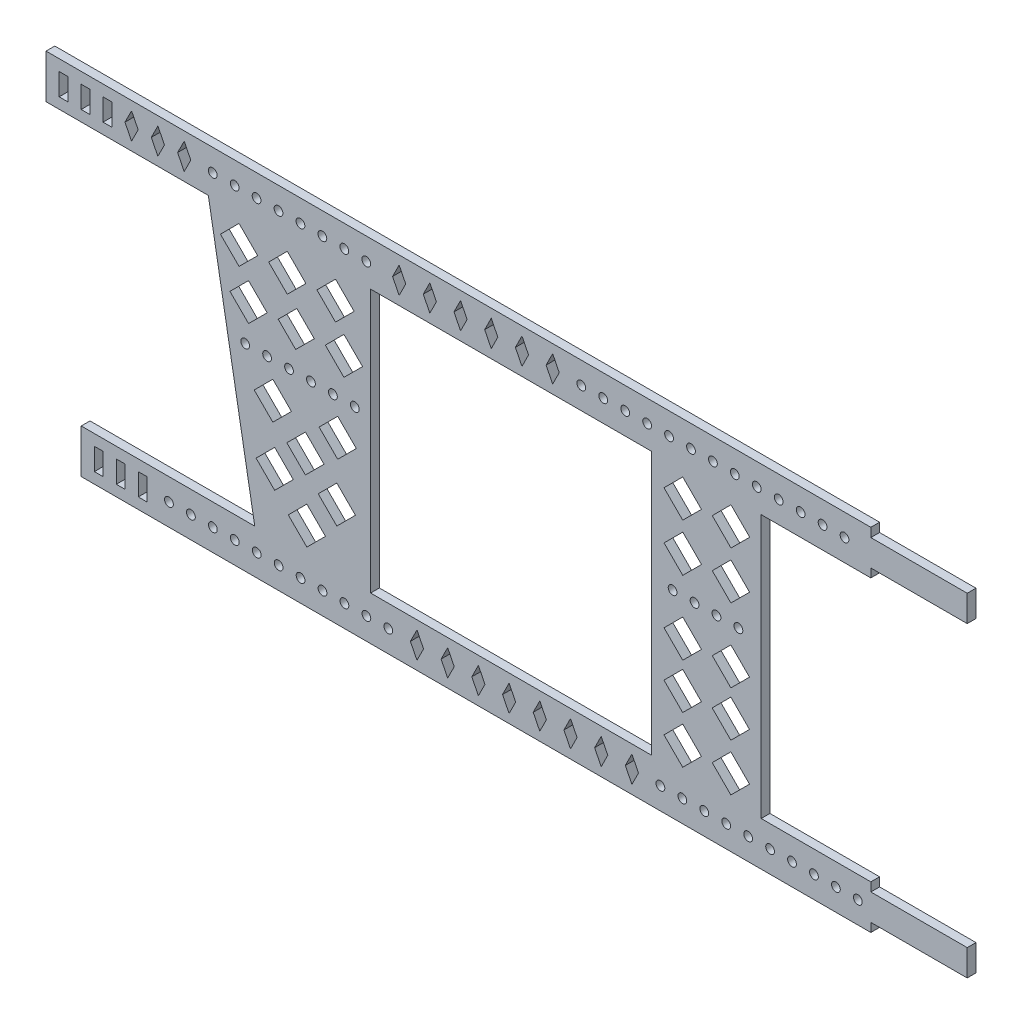
SolidWorks part; units mm, degrees
ref_plane "前视基准面" through (0, 0, 0) normal (0, 0, 1) x (1, 0, 0)
ref_plane "上视基准面" through (0, 0, 0) normal (0, 1, 0) x (1, 0, 0)
ref_plane "右视基准面" through (0, 0, 0) normal (1, 0, 0) x (0, 0, -1)
other "Configuration Table"
sketch "草图1" plane through (0, 0, 0) normal (0, 0, 1) x (1, 0, 0)
  line L4 (-82, 0.0001) -> (-80.5, 3.0002)
  line L11 (0, 0) -> (121.948, 0) construction
  line L17 (-82, 0.0001) -> (-80.4999, -3.0001)
  line L18 (-80.5, 3.0002) -> (-78.9999, 0)
  line L44 (-80.4999, -3.0001) -> (-78.9999, 0)
  line L49 (-76, 0.0001) -> (-74.5, 3.0002)
  line L50 (-92, 2.5) -> (-92, -2.5)
  line L51 (-99.9999, 5.0353) -> (88.0306, 5.0353)
  line L52 (-99.9999, 5.0353) -> (-99.9999, -4.9647)
  line L53 (-99.9999, -4.9647) -> (88.0306, -4.9647)
  line L54 (110.0001, 3) -> (110.0001, -3)
  line L55 (-97, 2.5) -> (-95, 2.5)
  line L56 (-97, 2.5) -> (-97, -2.5)
  line L57 (-97, -2.5) -> (-95, -2.5)
  line L58 (-95, 2.5) -> (-95, -2.5)
  line L59 (-97, 2.5) -> (-95, -2.5) construction
  line L60 (-97, -2.5) -> (-95, 2.5) construction
  line L61 (-92, 2.5) -> (-90, 2.5)
  line L62 (-90, 2.5) -> (-90, -2.5)
  line L63 (-92, -2.5) -> (-90, -2.5)
  line L64 (-87, 2.5) -> (-87, -2.5)
  line L65 (-87, 2.5) -> (-85, 2.5)
  line L66 (-85, 2.5) -> (-85, -2.5)
  line L67 (-87, -2.5) -> (-85, -2.5)
  line L72 (-76, 0.0001) -> (-74.4999, -3.0001)
  line L73 (-62.9999, -4.9647) -> (-52.4203, -64.9647)
  line L74 (-52.4203, -64.9647) -> (-25.9999, -64.9647)
  line L75 (-25.9999, -4.9647) -> (-25.9999, -64.9647)
  line L77 (-74.4999, -3.0001) -> (-72.9999, 0)
  line L78 (-74.5, 3.0002) -> (-72.9999, 0)
  line L79 (-70, 0.0001) -> (-68.5, 3.0002)
  line L80 (-70, 0.0001) -> (-68.4999, -3.0001)
  line L81 (-68.4999, -3.0001) -> (-66.9999, 0)
  line L82 (-68.5, 3.0002) -> (-66.9999, 0)
  line L83 (-61.9999, 0) -> (-56.9999, 0) construction
  line L84 (-62.9999, 0) -> (-62.9999, -4.9647) construction
  line L85 (-25.9999, 0) -> (-25.9999, -8.8507) construction
  line L86 (-21, 0.04) -> (-19.5, 3.04)
  line L87 (-21, 0.04) -> (-19.5, -2.96)
  line L88 (-19.5, -2.96) -> (-18, 0.04)
  line L89 (-19.5, 3.04) -> (-18, 0.04)
  line L90 (-14, 0.04) -> (-12.5, 3.04)
  line L91 (-12.5, 3.04) -> (-11, 0.04)
  line L92 (-12.5, -2.96) -> (-11, 0.04)
  line L93 (-14, 0.04) -> (-12.5, -2.96)
  line L94 (-7, 0.04) -> (-5.5, 3.04)
  line L95 (-5.5, 3.04) -> (-4, 0.04)
  line L96 (-5.5, -2.96) -> (-4, 0.04)
  line L97 (-7, 0.04) -> (-5.5, -2.96)
  line L98 (0, 0.04) -> (1.5, 3.04)
  line L99 (1.5, 3.04) -> (3, 0.04)
  line L100 (1.5, -2.96) -> (3, 0.04)
  line L101 (0, 0.04) -> (1.5, -2.96)
  line L102 (7, 0.04) -> (8.5, 3.04)
  line L103 (8.5, 3.04) -> (10, 0.04)
  line L104 (8.5, -2.96) -> (10, 0.04)
  line L105 (7, 0.04) -> (8.5, -2.96)
  line L106 (14, 0.04) -> (15.5, 3.04)
  line L107 (15.5, 3.04) -> (17, 0.04)
  line L108 (15.5, -2.96) -> (17, 0.04)
  line L109 (14, 0.04) -> (15.5, -2.96)
  line L110 (-21, 0.04) -> (-14, 0.04) construction
  line L111 (22.0306, 0.0331) -> (27.0306, 0.0331) construction
  line L112 (88.0306, 6.2733) -> (88.0306, -6.7746) construction
  line L113 (88.0306, 3) -> (110.0001, 3)
  line L114 (88.0306, -3) -> (110.0001, -3)
  line L115 (88.0306, 5.0353) -> (88.0306, 3)
  line L116 (88.0306, -3) -> (88.0306, -4.9647)
  line L117 (38.0306, 0.0331) -> (38.0306, -8.8507) construction
  line L118 (63.0306, 0.0331) -> (63.0306, -8.8507) construction
  line L138 (-55.9986, -6.9922) -> (-60.2412, -11.2349)
  line L143 (-44.9986, -6.9922) -> (-49.2412, -11.2349)
  line L144 (-44.9986, -6.9922) -> (-40.7559, -11.2349)
  line L145 (-55.9986, -6.9922) -> (-51.7559, -11.2349)
  line L146 (-60.2412, -11.2349) -> (-55.9986, -15.4775)
  line L147 (-51.7559, -11.2349) -> (-55.9986, -15.4775)
  line L148 (-40.7559, -11.2349) -> (-44.9986, -15.4775)
  line L149 (-49.2412, -11.2349) -> (-44.9986, -15.4775)
  line L150 (-33.9986, -6.9922) -> (-38.2412, -11.2349)
  line L151 (-33.9986, -6.9922) -> (-29.7559, -11.2349)
  line L152 (-29.7559, -11.2349) -> (-33.9986, -15.4775)
  line L153 (-38.2412, -11.2349) -> (-33.9986, -15.4775)
  line L154 (-55.9986, -6.9922) -> (-44.9986, -6.9922) construction
  line L167 (-53.8279, -17.1935) -> (-58.0705, -21.4361)
  line L168 (-42.8279, -17.1935) -> (-47.0705, -21.4361)
  line L169 (-42.8279, -17.1935) -> (-38.8399, -21.1815)
  line L170 (-53.8279, -17.1935) -> (-49.5852, -21.4361)
  line L171 (-58.0705, -21.4361) -> (-53.8279, -25.6788)
  line L172 (-49.5852, -21.4361) -> (-53.8279, -25.6788)
  line L173 (-38.8399, -21.1815) -> (-43.0826, -25.4241)
  line L174 (-47.0705, -21.4361) -> (-43.0826, -25.4241)
  line L175 (-32.0826, -16.9388) -> (-36.3252, -21.1815)
  line L176 (-32.0826, -16.9388) -> (-27.8399, -21.1815)
  line L177 (-27.8399, -21.1815) -> (-32.0826, -25.4241)
  line L178 (-36.3252, -21.1815) -> (-32.0826, -25.4241)
  line L179 (-53.8279, -17.1935) -> (-42.8279, -17.1935) construction
  line L180 (63.0306, -29.9647) -> (-66.6645, -29.9647) construction
  line L181 (-54.5983, -30) -> (-49.5983, -30) construction
  line L186 (-48.294, -33.8993) -> (-52.5367, -38.1419)
  line L187 (-52.5367, -38.1419) -> (-48.294, -42.3846)
  line L188 (-44.0514, -38.1419) -> (-48.294, -42.3846)
  line L189 (-48.294, -33.8993) -> (-44.0514, -38.1419)
  line L190 (-33.5054, -33.8232) -> (-37.7481, -38.0658)
  line L191 (-37.7481, -38.0658) -> (-33.5054, -42.3084)
  line L192 (-29.2628, -38.0658) -> (-33.5054, -42.3084)
  line L193 (-33.5054, -33.8232) -> (-29.2628, -38.0658)
  line L195 (-47.8719, -47.1411) -> (-52.1146, -51.3837)
  line L196 (-52.1146, -51.3837) -> (-47.8719, -55.6263)
  line L197 (-43.6293, -51.3837) -> (-47.8719, -55.6263)
  line L198 (-47.8719, -47.1411) -> (-43.6293, -51.3837)
  line L199 (-40.8637, -40.6049) -> (-45.1063, -44.8475)
  line L200 (-45.1063, -44.8475) -> (-40.8637, -49.0901)
  line L201 (-36.6211, -44.8475) -> (-40.8637, -49.0901)
  line L202 (-40.8637, -40.6049) -> (-36.6211, -44.8475)
  line L203 (-40.5381, -54.6754) -> (-44.7807, -58.9181)
  line L204 (-44.7807, -58.9181) -> (-40.5381, -63.1607)
  line L205 (-36.2954, -58.9181) -> (-40.5381, -63.1607)
  line L206 (-40.5381, -54.6754) -> (-36.2954, -58.9181)
  line L207 (-33.7086, -47.1027) -> (-37.9513, -51.3454)
  line L208 (-37.9513, -51.3454) -> (-33.7086, -55.588)
  line L209 (-29.466, -51.3454) -> (-33.7086, -55.588)
  line L210 (-33.7086, -47.1027) -> (-29.466, -51.3454)
  line L215 (-52.4203, -64.9647) -> (-91.9694, -64.9647)
  line L216 (-25.9999, -64.9647) -> (63.0306, -64.9647)
  line L217 (38.0306, -4.9647) -> (38.0306, -64.9647)
  line L218 (63.0306, 0) -> (63.0306, -64.9647)
  line L219 (42.8446, -29.9642) -> (47.8446, -29.9642) construction
  line L220 (45.1493, -6.4688) -> (40.8811, -10.737)
  line L221 (40.8811, -10.737) -> (45.1493, -15.0051)
  line L222 (49.4174, -10.737) -> (45.1493, -15.0051)
  line L223 (45.1493, -6.4688) -> (49.4174, -10.737)
  line L224 (56.1493, -6.4688) -> (51.8811, -10.737)
  line L225 (51.8811, -10.737) -> (56.1493, -15.0051)
  line L226 (60.4174, -10.737) -> (56.1493, -15.0051)
  line L227 (56.1493, -6.4688) -> (60.4174, -10.737)
  line L228 (45.1493, -6.4688) -> (56.1493, -6.4688) construction
  line L229 (45.1571, -17.3518) -> (40.889, -21.62)
  line L230 (40.889, -21.62) -> (45.1571, -25.8881)
  line L231 (49.4253, -21.62) -> (45.1571, -25.8881)
  line L232 (45.1571, -17.3518) -> (49.4253, -21.62)
  line L233 (56.1316, -17.3518) -> (51.8762, -21.6072)
  line L234 (51.8762, -21.6072) -> (56.1316, -25.8626)
  line L235 (60.387, -21.6072) -> (56.1316, -25.8626)
  line L236 (56.1316, -17.3518) -> (60.387, -21.6072)
  line L237 (45.1571, -17.3518) -> (56.1316, -17.3518) construction
  line L238 (45.1553, -34.115) -> (40.8872, -38.3832)
  line L239 (40.8872, -38.3832) -> (45.1553, -42.6513)
  line L240 (49.4235, -38.3832) -> (45.1553, -42.6513)
  line L241 (45.1553, -34.115) -> (49.4235, -38.3832)
  line L242 (56.1298, -34.1405) -> (51.8872, -38.3832)
  line L243 (51.8872, -38.3832) -> (56.1298, -42.6258)
  line L244 (60.3725, -38.3832) -> (56.1298, -42.6258)
  line L245 (56.1298, -34.1405) -> (60.3725, -38.3832)
  line L246 (45.1553, -34.115) -> (56.1298, -34.1405) construction
  line L247 (45.142, -44.4521) -> (40.8738, -48.7203)
  line L248 (40.8738, -48.7203) -> (45.142, -52.9884)
  line L249 (49.4101, -48.7203) -> (45.142, -52.9884)
  line L250 (45.142, -44.4521) -> (49.4101, -48.7203)
  line L251 (56.1165, -44.4521) -> (51.8611, -48.7075)
  line L252 (51.8611, -48.7075) -> (56.1165, -52.9629)
  line L253 (60.3719, -48.7075) -> (56.1165, -52.9629)
  line L254 (56.1165, -44.4521) -> (60.3719, -48.7075)
  line L255 (45.142, -44.4521) -> (56.1165, -44.4521) construction
  line L256 (45.146, -55.2548) -> (40.8778, -59.523)
  line L257 (40.8778, -59.523) -> (45.146, -63.7911)
  line L258 (49.4141, -59.523) -> (45.146, -63.7911)
  line L259 (45.146, -55.2548) -> (49.4141, -59.523)
  line L260 (56.1205, -55.2548) -> (51.8651, -59.5102)
  line L261 (51.8651, -59.5102) -> (56.1205, -63.7656)
  line L262 (60.3759, -59.5102) -> (56.1205, -63.7656)
  line L263 (56.1205, -55.2548) -> (60.3759, -59.5102)
  line L264 (45.146, -55.2548) -> (56.1205, -55.2548) construction
  line L265 (45.1493, -6.4943) -> (45.1493, -76.2288) construction
  line L266 (0, 0.04) -> (0, -21.1815) construction
  line L267 (-91.9694, -64.9647) -> (-91.9694, -74.9647)
  line L268 (-91.9694, -74.9647) -> (88.0306, -74.9647)
  line L269 (63.0306, -64.9647) -> (88.0306, -64.9647)
  line L270 (88.0306, -64.9647) -> (88.0306, -66.9647)
  line L271 (88.0306, -66.9647) -> (110.0001, -66.9647)
  line L272 (110.0001, -66.9647) -> (110.0001, -72.9647)
  line L273 (110.0001, -72.9647) -> (88.0306, -72.9647)
  line L274 (88.0306, -72.9647) -> (88.0306, -74.9647)
  line L275 (-83.9694, -67.4775) -> (-81.9694, -67.4775)
  line L276 (47.8446, -29.9642) -> (52.8446, -29.9642) construction
  line L277 (52.8446, -29.9642) -> (50.3446, -29.9642) construction
  line L278 (50.3446, -29.9642) -> (50.3446, -32.9055) construction
  line L279 (40.0646, -69.9647) -> (45.0646, -69.9647) construction
  line L283 (-88.9694, -67.4775) -> (-86.9694, -67.4775)
  line L284 (-88.9694, -67.4775) -> (-88.9694, -72.4775)
  line L285 (-88.9694, -72.4775) -> (-86.9694, -72.4775)
  line L286 (-86.9694, -67.4775) -> (-86.9694, -72.4775)
  line L287 (-88.9694, -67.4775) -> (-86.9694, -72.4775) construction
  line L288 (-88.9694, -72.4775) -> (-86.9694, -67.4775) construction
  line L304 (-81.9694, -67.4775) -> (-81.9694, -72.4775)
  line L305 (-83.9694, -72.4775) -> (-81.9694, -72.4775)
  line L306 (-83.9694, -67.4775) -> (-83.9694, -72.4775)
  line L307 (-78.9694, -67.4775) -> (-76.9694, -67.4775)
  line L308 (-76.9694, -67.4775) -> (-76.9694, -72.4775)
  line L309 (-78.9694, -72.4775) -> (-76.9694, -72.4775)
  line L310 (-78.9694, -67.4775) -> (-78.9694, -72.4775)
  line L311 (-88.9694, -67.4775) -> (-83.9694, -67.4775) construction
  line L312 (-90.9389, -69.9647) -> (-66.4869, -69.9647) construction
  line L313 (-71.9694, -69.9647) -> (-66.9694, -69.9647) construction
  line L314 (-16.9354, -69.9662) -> (-15.4354, -66.9662)
  line L315 (-15.4354, -66.9662) -> (-13.9354, -69.9662)
  line L316 (-15.4354, -72.9662) -> (-13.9354, -69.9662)
  line L317 (-16.9354, -69.9662) -> (-15.4354, -72.9662)
  line L318 (-9.9354, -69.9662) -> (-8.4354, -66.9662)
  line L319 (-8.4354, -66.9662) -> (-6.9354, -69.9662)
  line L320 (-8.4354, -72.9662) -> (-6.9354, -69.9662)
  line L321 (-9.9354, -69.9662) -> (-8.4354, -72.9662)
  line L322 (-2.9354, -69.9662) -> (-1.4354, -66.9662)
  line L323 (-1.4354, -66.9662) -> (0.0646, -69.9662)
  line L324 (-1.4354, -72.9662) -> (0.0646, -69.9662)
  line L325 (-2.9354, -69.9662) -> (-1.4354, -72.9662)
  line L326 (4.0646, -69.9662) -> (5.5646, -66.9662)
  line L327 (5.5646, -66.9662) -> (7.0646, -69.9662)
  line L328 (5.5646, -72.9662) -> (7.0646, -69.9662)
  line L329 (4.0646, -69.9662) -> (5.5646, -72.9662)
  line L330 (11.0646, -69.9662) -> (12.5646, -66.9662)
  line L331 (12.5646, -66.9662) -> (14.0646, -69.9662)
  line L332 (12.5646, -72.9662) -> (14.0646, -69.9662)
  line L333 (11.0646, -69.9662) -> (12.5646, -72.9662)
  line L334 (18.0646, -69.9662) -> (19.5646, -66.9662)
  line L335 (19.5646, -66.9662) -> (21.0646, -69.9662)
  line L336 (19.5646, -72.9662) -> (21.0646, -69.9662)
  line L337 (18.0646, -69.9662) -> (19.5646, -72.9662)
  line L338 (25.0646, -69.9662) -> (26.5646, -66.9662)
  line L339 (26.5646, -66.9662) -> (28.0646, -69.9662)
  line L340 (26.5646, -72.9662) -> (28.0646, -69.9662)
  line L341 (25.0646, -69.9662) -> (26.5646, -72.9662)
  line L342 (32.0646, -69.9662) -> (33.5646, -66.9662)
  line L343 (33.5646, -66.9662) -> (35.0646, -69.9662)
  line L344 (33.5646, -72.9662) -> (35.0646, -69.9662)
  line L345 (32.0646, -69.9662) -> (33.5646, -72.9662)
  line L346 (-16.9354, -69.9662) -> (-9.9354, -69.9662) construction
  circle A0 centre (-61.9999, 0) radius 1
  circle A1 centre (-56.9999, 0) radius 1
  circle A2 centre (-51.9999, 0) radius 1
  circle A3 centre (-46.9999, 0) radius 1
  circle A4 centre (-41.9999, 0) radius 1
  circle A5 centre (-36.9999, 0) radius 1
  circle A6 centre (-31.9999, 0) radius 1
  circle A7 centre (-26.9999, 0) radius 1
  circle A8 centre (22.0306, 0.0331) radius 1
  circle A9 centre (27.0306, 0.0331) radius 1
  circle A10 centre (32.0306, 0.0331) radius 1
  circle A11 centre (37.0306, 0.0331) radius 1
  circle A12 centre (42.0306, 0.0331) radius 1
  circle A13 centre (47.0306, 0.0331) radius 1
  circle A14 centre (52.0306, 0.0331) radius 1
  circle A15 centre (57.0306, 0.0331) radius 1
  circle A16 centre (62.0306, 0.0331) radius 1
  circle A17 centre (67.0306, 0.0331) radius 1
  circle A18 centre (72.0306, 0.0331) radius 1
  circle A19 centre (77.0306, 0.0331) radius 1
  circle A20 centre (82.0306, 0.0331) radius 1
  circle A21 centre (-55.9986, -11.2349) radius 4.2426 construction
  circle A23 centre (-53.8279, -21.4361) radius 4.2426 construction
  circle A24 centre (-54.5983, -30) radius 1
  circle A25 centre (-49.5983, -30) radius 1
  circle A26 centre (-44.5983, -30) radius 1
  circle A27 centre (-39.5983, -30) radius 1
  circle A28 centre (-34.5983, -30) radius 1
  circle A29 centre (-29.5983, -30) radius 1
  circle A30 centre (42.8446, -29.9642) radius 1
  circle A31 centre (47.8446, -29.9642) radius 1
  circle A32 centre (52.8446, -29.9642) radius 1
  circle A33 centre (57.8446, -29.9642) radius 1
  circle A38 centre (-71.9694, -69.9647) radius 1
  circle A39 centre (-66.9694, -69.9647) radius 1
  circle A40 centre (-61.9694, -69.9647) radius 1
  circle A41 centre (-56.9694, -69.9647) radius 1
  circle A42 centre (-51.9694, -69.9647) radius 1
  circle A43 centre (-46.9694, -69.9647) radius 1
  circle A44 centre (-41.9694, -69.9647) radius 1
  circle A45 centre (-36.9694, -69.9647) radius 1
  circle A46 centre (-31.9694, -69.9647) radius 1
  circle A47 centre (-26.9694, -69.9647) radius 1
  circle A48 centre (-21.9694, -69.9647) radius 1
  circle A50 centre (-16.9694, -69.9647) radius 1 [skipped]
  circle A51 centre (40.0646, -69.9647) radius 1
  circle A52 centre (45.0646, -69.9647) radius 1
  circle A53 centre (50.0646, -69.9647) radius 1
  circle A54 centre (55.0646, -69.9647) radius 1
  circle A55 centre (60.0646, -69.9647) radius 1
  circle A56 centre (65.0646, -69.9647) radius 1
  circle A57 centre (70.0646, -69.9647) radius 1
  circle A58 centre (75.0646, -69.9647) radius 1
  circle A59 centre (80.0646, -69.9647) radius 1
  circle A60 centre (85.0646, -69.9647) radius 1
  point P0 (0, 0)
  point P11 (-61.9999, 0)
  point P32 (0, 0)
  point P33 (-96, 0)
  point P35 (0, 0)
  point P40 (-99.9999, 0.0353)
  point P41 (-96, 0)
  point P46 (-82, 0.0001)
  point P60 (-20.9999, 0)
  point P74 (22, 0)
  point P100 (88.0306, 0)
  point P128 (88.0306, -3)
  point P129 (88.0306, 3)
  point P130 (88.0306, 0)
  point P133 (88.0306, 5.0353)
  point P136 (88.0306, -4.9647)
  point P169 (-25.9999, -29.9647)
  point P172 (-54.5983, -29.9647)
  point P225 (42.8454, -29.9647)
  point P291 (88.0306, -64.9647)
  point P307 (40.0646, -69.9647)
  point P319 (-87.9694, -69.9775)
  point P320 (-87.9694, -69.9775)
  point P332 (-71.9694, -69.9647)
  point P333 (-91.9694, -69.9647)
  dimension "D7" = 2
  dimension "D32" = 8.4853
  dimension "D34" = 8.4853
  dimension "D43" = 11
  dimension "D58" = 2
  dimension "D64" = 2
  dimension "D2" = 3
  dimension "D3" = 3
  dimension "D4" = 3
  dimension "D5" = 33
  dimension "D8" = 5
  dimension "D9" = 210
  dimension "D10" = 10
  dimension "D11" = 4
  dimension "D12" = 2
  dimension "D13" = 5
  dimension "D15" = 8
  dimension "D6" = 5
  dimension "D16" = 5
  dimension "D18" = 7
  dimension "D19" = 5
  dimension "D20" = 5
  dimension "D21" = 182.0305
  dimension "D22" = 6
  dimension "D23" = 3
  dimension "D24" = 3
  dimension "D25" = 21.9695
  dimension "D26" = 137.0305
  dimension "D28" = 100
  dimension "D29" = 60
  dimension "D30" = 11
  dimension "D31" = 3
  dimension "D33" = 6
  dimension "D35" = 6
  dimension "D36" = 5
  dimension "D37" = 25
  dimension "D38" = 6
  dimension "D39" = 6
  dimension "D41" = 5
  dimension "D44" = 2
  dimension "D42" = 60
  dimension "D45" = 10
  dimension "D46" = 2
  dimension "D47" = 180
  dimension "D48" = 2
  dimension "D49" = 21.9695
  dimension "D50" = 6
  dimension "D52" = 5
  dimension "D53" = 4
  dimension "D54" = 5
  dimension "D55" = 5
  dimension "D57" = 5
  dimension "D59" = 5
  dimension "D61" = 12
  dimension "D62" = 7
  dimension "D63" = 5
  dimension "D65" = 5
  dimension "D14" = 3
  dimension "D17" = 3
  dimension "D60" = 6
  dimension "D27" = 13
  dimension "D51" = 4
  dimension "D56" = 3
extrude "凸台-拉伸1" add sketch "草图1" along normal blind 2
